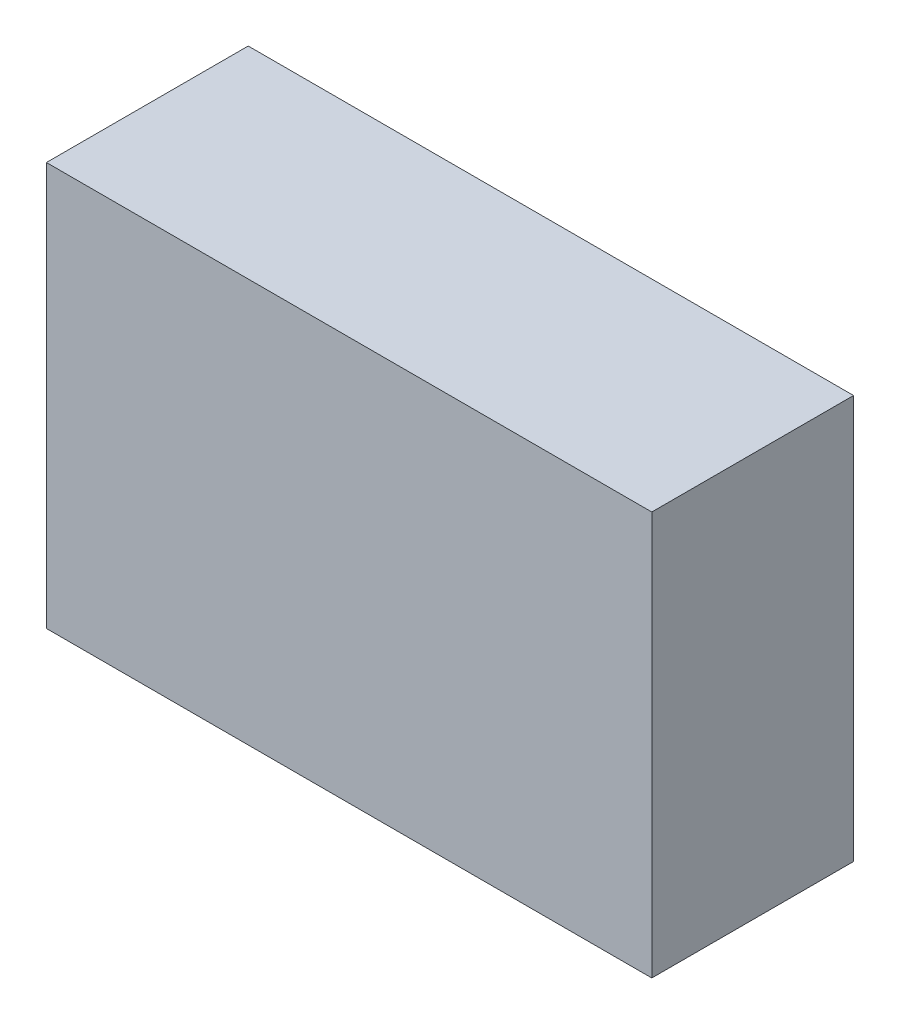
SolidWorks part; units mm, degrees
ref_plane "Ebene vorne" through (0, 0, 0) normal (0, 0, 1) x (1, 0, 0)
ref_plane "Ebene oben" through (0, 0, 0) normal (0, 1, 0) x (1, 0, 0)
ref_plane "Ebene rechts" through (0, 0, 0) normal (1, 0, 0) x (0, 0, -1)
sketch "Skizze1" plane through (0, 0, 0) normal (0, 1, 0) x (1, 0, 0)
  line L1 (0, 0) -> (3, 0)
  line L2 (0, 0) -> (0, -1)
  line L3 (0, -1) -> (3, -1)
  line L4 (3, 0) -> (3, -1)
  dimension "D1" = 3
  dimension "D2" = 1
extrude "Aufsatz-Linear austragen1" add sketch "Skizze1" along normal blind 2
